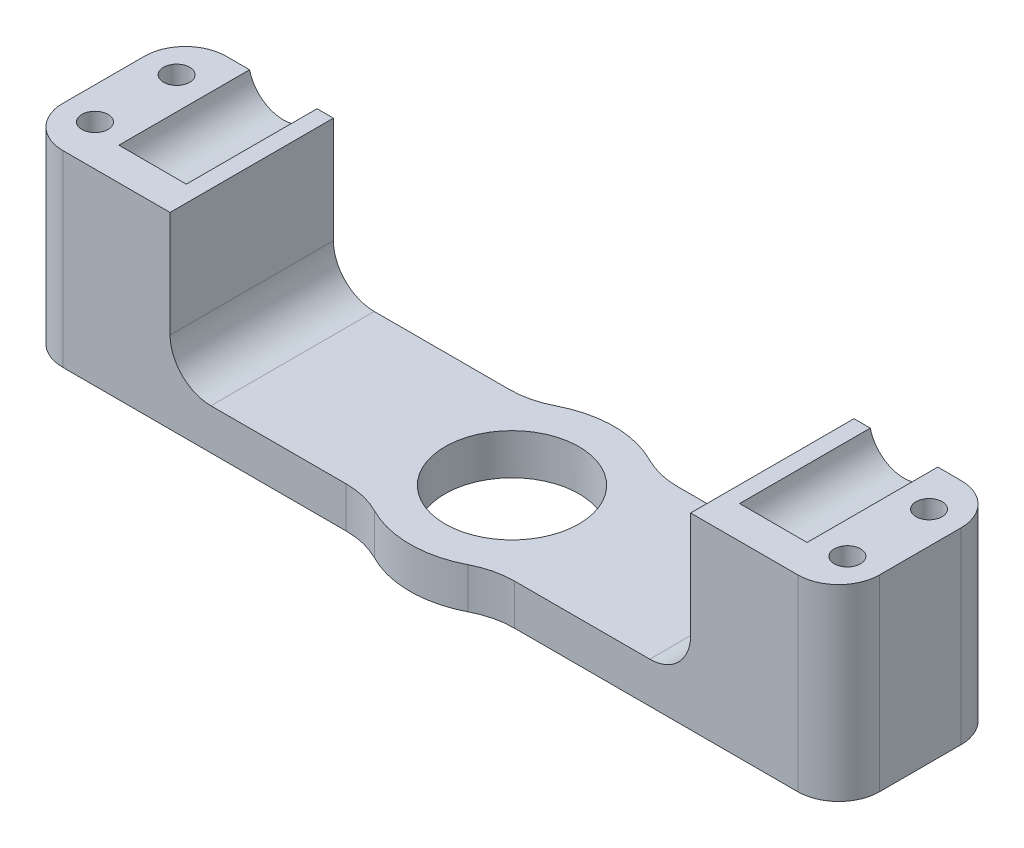
SolidWorks part; units mm, degrees
ref_plane "Front Plane" through (0, 0, 0) normal (0, 0, 1) x (1, 0, 0)
ref_plane "Top Plane" through (0, 0, 0) normal (0, 1, 0) x (1, 0, 0)
ref_plane "Right Plane" through (0, 0, 0) normal (1, 0, 0) x (0, 0, -1)
sketch "Sketch1" plane through (0, 0, 0) normal (0, 1, 0) x (1, 0, 0)
  line L0 (-44, 0) -> (-44, -44) construction
  line L1 (-44, -44) -> (44, -44) construction
  line L2 (44, -44) -> (44, 0) construction
  line L4 (-44, -10) -> (44, -10)
  line L5 (-44, -10) -> (-44, 10)
  line L6 (-44, 10) -> (44, 10)
  line L7 (44, -10) -> (44, 10)
  line L8 (-44, -10) -> (44, 10) construction
  line L9 (-44, 10) -> (44, -10) construction
  arc A0 (44, 0) -> (-44, 0) centre (0, 0) ccw construction
  dimension "D1" = 88
  dimension "D2" = 88
  dimension "D3" = 20
extrude "Boss-Extrude1" add sketch "Sketch1" along normal blind 48
sketch "Sketch2" plane through (0, 0, 10) normal (0, 0, 1) x (1, 0, 0)
  line L1 (-1044, 24) -> (48956, 24) construction
  line L2 (0, -1000) -> (0, 49000) construction
  line L3 (-44, 48) -> (-44, 0) construction
  circle A0 centre (-38, 24) radius 4.25
  circle A1 centre (38, 24) radius 4.25
  point P2 (-44, 24)
  dimension "D1" = 8.5
  dimension "D2" = 6
extrude "Cut-Extrude1" cut sketch "Sketch2" against normal through all
sketch "Sketch7" plane through (0, 48, 0) normal (0, 1, 0) x (1, 0, 0)
  circle A0 centre (0, 0) radius 12.5
  dimension "D1" = 25
extrude "Boss-Extrude2" add sketch "Sketch7" against normal up to surface (48 mm away) up to face at (0, 0, 0)
sketch "Sketch4" plane through (0, 48, 0) normal (0, 1, 0) x (1, 0, 0)
  circle A0 centre (0, 0) radius 8.2
  dimension "D1" = 16.4
extrude "Cut-Extrude3" cut sketch "Sketch4" against normal through all
fillet "Fillet2" radius 10 4 edges at (-7.5, 24, 10) (7.5, 24, 10) (7.5, 24, -10) (-7.5, 24, -10)
sketch "Sketch9" plane through (-44, 0, 0) normal (-1, 0, 0) x (0, 0, 1)
  line L5 (-1017.3065, 48) -> (48982.6935, 48) construction
  line L6 (-1016.9067, 23) -> (48983.0933, 23) construction
  line L7 (-12.5, 48) -> (-12.5, 0) construction
  line L8 (-10, 48) -> (10, 48) construction
  line L9 (12.5, 0) -> (12.5, 48) construction
  line L10 (-13.5, 48) -> (13.5, 48)
  line L11 (-13.5, 48) -> (-13.5, 23)
  line L12 (-13.5, 23) -> (13.5, 23)
  line L13 (13.5, 48) -> (13.5, 23)
  line L14 (-12.5, 48) -> (-12.5, 0) construction
  point P3 (-12.5, 23)
  point P21 (-12.5, 24)
  dimension "D1" = 1
  dimension "D2" = 1
  dimension "D3" = 1
extrude "Cut-Extrude4" cut sketch "Sketch9" against normal through all
sketch "Sketch10" plane through (0, 0, 0) normal (0, 0, 1) x (1, 0, 0)
  line L0 (44, 0) -> (10.3078, 0) construction
  line L1 (31.8693, 25) -> (-31.8693, 25)
  line L2 (31.8693, 25) -> (31.8693, 5)
  line L3 (31.8693, 5) -> (-31.8693, 5)
  line L4 (-31.8693, 25) -> (-31.8693, 5)
  line L5 (10.3078, 23) -> (33.8693, 23) construction
  dimension "D1" = 5
  dimension "D2" = 2
  dimension "D3" = 2
  dimension "D4" = 2
extrude "Cut-Extrude5" cut sketch "Sketch10" against normal through all and the other way through all
fillet "Fillet3" radius 5 2 edges at (-31.8693, 5, 0) (31.8693, 5, 0)
sketch "Sketch11" plane through (44, 0, 0) normal (1, 0, 0) x (0, 0, -1)
  line L4 (10, 0) -> (10, 23)
  line L5 (10, 23) -> (-10, 23)
  line L6 (-10, 23) -> (-10, 0)
  line L7 (-10, 0) -> (10, 0)
  line L8 (10, 0) -> (10, 23)
  line L9 (10, 23) -> (-10, 23)
  line L10 (-10, 23) -> (-10, 0)
  line L11 (-10, 0) -> (10, 0)
  dimension "D1" = 0
extrude "Boss-Extrude3" add sketch "Sketch11" along normal blind 6
sketch "Sketch12" plane through (0, 23, 0) normal (0, 1, 0) x (1, 0, 0)
  line L0 (50, -10) -> (42.1307, -10) construction
  line L1 (42.1307, 10) -> (50, 10) construction
  circle A0 centre (46.0653, 5) radius 1.6
  circle A1 centre (46.0653, -5) radius 1.6
  point P4 (46.0653, -10)
  dimension "D1" = 3.2
  dimension "D2" = 5
  dimension "D3" = 5
extrude "Cut-Extrude6" cut sketch "Sketch12" against normal through all
mirror "Mirror1" about plane through (0, 0, 0) normal (1, 0, 0) of "Cut-Extrude6", "Boss-Extrude3"
fillet "Fillet5" radius 5 4 edges at (-50, 11.5, -10) (-50, 11.5, 10) (50, 11.5, 10) (50, 11.5, -10)
sketch "Sketch13" plane through (0, 0, 10) normal (0, 0, 1) x (1, 0, 0)
  line L0 (-42.1307, 23) -> (-33.8693, 23)
  line L1 (33.8693, 23) -> (42.1307, 23)
  arc A0 (33.8693, 23) -> (42.1307, 23) centre (38, 24) ccw construction
  arc A1 (33.8693, 23) -> (42.1307, 23) centre (38, 24) ccw
  arc A2 (-42.1307, 23) -> (-33.8693, 23) centre (-38, 24) ccw construction
  arc A3 (-42.1307, 23) -> (-33.8693, 23) centre (-38, 24) ccw
extrude "Boss-Extrude4" add sketch "Sketch13" against normal blind 4
